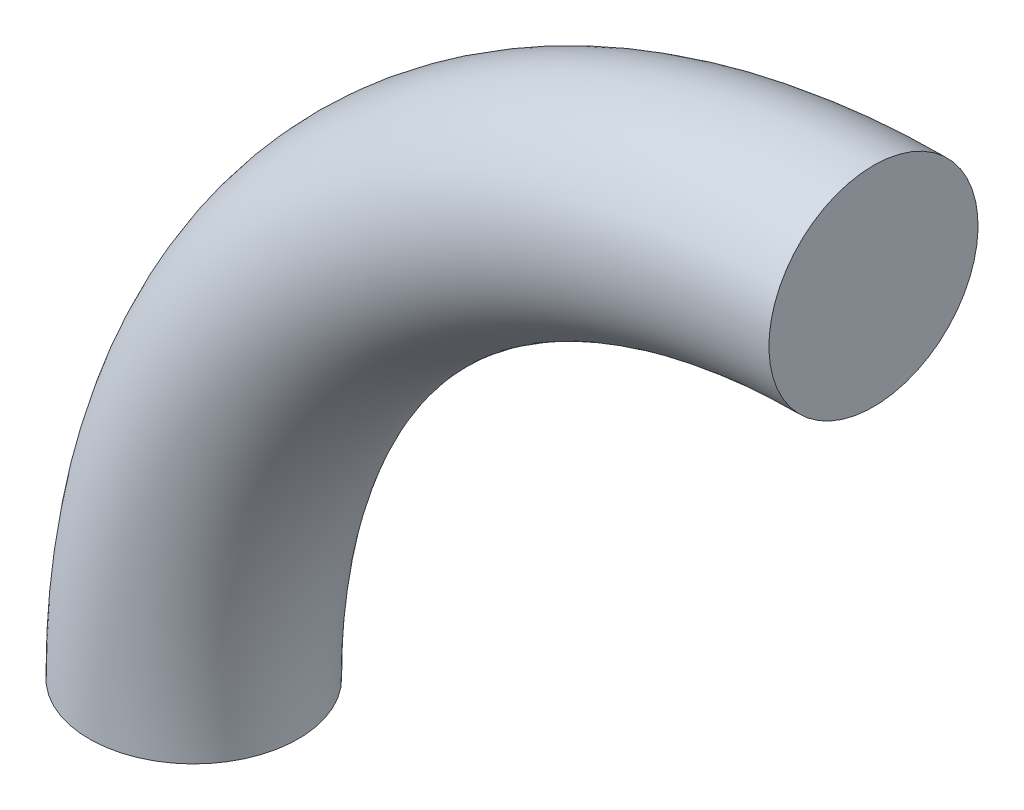
SolidWorks part; units mm, degrees
ref_plane "Front Plane" through (0, 0, 0) normal (0, 0, 1) x (1, 0, 0)
ref_plane "Top Plane" through (0, 0, 0) normal (0, 1, 0) x (1, 0, 0)
ref_plane "Right Plane" through (0, 0, 0) normal (1, 0, 0) x (0, 0, -1)
sketch "Sketch1" plane through (0, 0, 0) normal (0, 0, 1) x (1, 0, 0)
  line L0 (0, 0) -> (0, -22.0953) construction
  line L1 (65, 65) -> (94.9364, 65) construction
  arc A0 (0, 0) -> (65, 65) centre (65, 0) cw
  dimension "D1" = 65
sketch "Sketch2" plane through (0, 0, 0) normal (0, 1, 0) x (1, 0, 0)
  circle A0 centre (0, 0) radius 10
  dimension "D1" = 20
sweep "Sweep1" add profiles "Sketch2" path "Sketch1"
